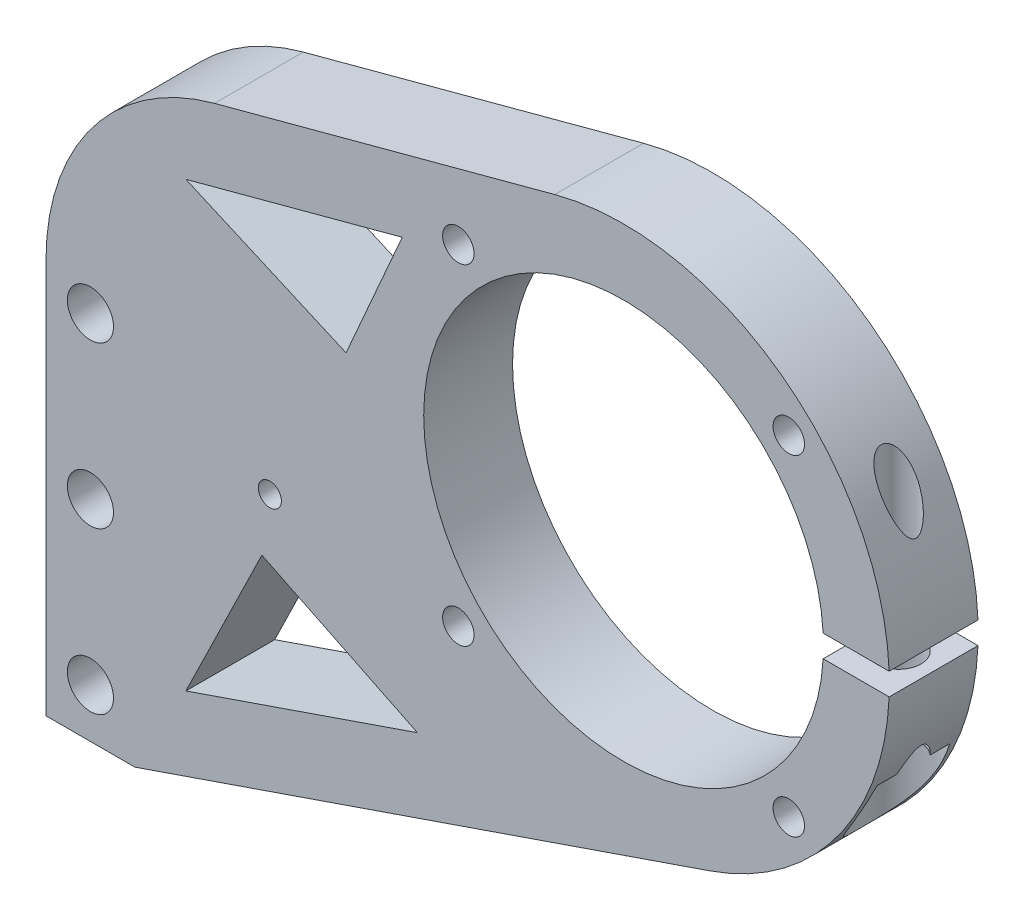
SolidWorks part; units mm, degrees
ref_plane "Front Plane" through (0, 0, 0) normal (0, 0, 1) x (1, 0, 0)
ref_plane "Top Plane" through (0, 0, 0) normal (0, 1, 0) x (1, 0, 0)
ref_plane "Right Plane" through (0, 0, 0) normal (1, 0, 0) x (0, 0, -1)
ref_plane "Plane1" through (0, 0, 0) normal (0, 0, -1) x (-1, 0, 0)
sketch "Sketch1" plane through (0, 0, 0) normal (0, 0, -1) x (-1, 0, 0)
  line L0 (224.1695, 127.7225) -> (151.4352, 147.2116)
  line L1 (129.2465, 74.5705) -> (211.4695, 46.305)
  line L2 (211.4695, 46.305) -> (224.1695, 46.305)
  line L3 (224.1695, 46.305) -> (224.1695, 127.7225)
  arc A0 (151.4352, 147.2116) -> (129.2465, 74.5705) centre (141.6001, 110.5064) ccw
extrude "Boss-Extrude1" add sketch "Sketch1" against normal blind 12.7
sketch "Sketch2" plane through (0, 0, 12.7) normal (0, 0, 1) x (1, 0, 0)
  line L0 (-103.6333, 112.0939) -> (-113.179, 112.0939)
  line L1 (-113.179, 108.9189) -> (-103.6333, 108.9189)
  arc A0 (-103.6333, 108.9189) -> (-103.6333, 112.0939) centre (-141.6001, 110.5064) ccw
  arc A1 (-113.179, 112.0939) -> (-113.179, 108.9189) centre (-141.6001, 110.5064) cw
extrude "Cut-Extrude1" cut sketch "Sketch2" against normal through all
ref_plane "Plane2" through (0, 110.5064, 0) normal (0, 1, 0) x (1, 0, 0)
sketch "Sketch3" plane through (0, 110.5064, 0) normal (0, 1, 0) x (1, 0, 0)
  line L0 (-113.0251, 0) -> (-141.6001, 0)
  line L1 (-141.6001, 0) -> (-141.6001, -12.7)
  line L2 (-141.6001, -12.7) -> (-113.0251, -12.7)
  line L3 (-113.0251, -12.7) -> (-113.0251, 0)
  line L4 (-141.6001, 0) -> (-141.6001, -12.7) construction
  dimension "D1" = 28.575
revolve "Cut-Revolve1" cut sketch "Sketch3" angle 360 about L4
hole_wizard "#8 Clearance Hole1" positions "Sketch5" profile "Sketch4" hole size "#8" standard "ANSI Inch"
sketch "Sketch5" plane through (0, 0, 12.7) normal (0, 0, 1) x (1, 0, 0)
  line L0 (-141.6001, 139.0814) -> (-141.6001, 81.9314) construction
  arc A0 (-113.0692, 112.0939) -> (-113.0692, 108.9189) centre (-141.6001, 110.5064) ccw construction
  point P0 (-117.9781, 86.8844)
  point P1 (-165.2221, 86.8844)
  point P2 (-165.2221, 134.1284)
  point P3 (-117.9781, 134.1284)
  point P12 (-141.6001, 110.5064)
  dimension "D1" = 47.244
  dimension "D2" = 47.244
  dimension "D3" = 23.622
  dimension "D4" = 47.244
  dimension "D5" = 23.622
  dimension "D6" = 23.622
  dimension "D7" = 47.244
  dimension "D8" = 23.622
sketch "Sketch4" plane through (-117.9781, 86.8844, 12.7) normal (1, 0, 0) x (0, -1, 0)
  line L0 (0, 0) -> (0, 12.7)
  line L1 (0, 12.7) -> (2.25, 12.7)
  line L2 (2.25, 12.7) -> (2.25, 0)
  line L5 (2.25, 0) -> (0, 0)
  line L11 (0, -6.35) -> (0, 107.95) construction
  dimension "Thru Hole Dia." = 4.5
  dimension "Thru Hole Depth" = 12.7
hole_wizard "1/4 Clearance Hole1" positions "Sketch7" profile "Sketch6" hole size "1/4" standard "ANSI Inch"
sketch "Sketch7" plane through (0, 0, 0) normal (0, 0, -1) x (-1, 0, 0)
  point P0 (217.8195, 53.305)
  point P1 (217.8195, 76.305)
  point P2 (217.8195, 99.305)
sketch "Sketch6" plane through (-217.8195, 53.305, 0) normal (1, 0, 0) x (0, 1, 0)
  line L0 (0, 0) -> (0, 12.7)
  line L1 (0, 12.7) -> (3.3, 12.7)
  line L2 (3.3, 12.7) -> (3.3, 0)
  line L5 (3.3, 0) -> (0, 0)
  line L11 (0, -6.35) -> (0, 107.95) construction
  dimension "Thru Hole Dia." = 6.6
  dimension "Thru Hole Depth" = 12.7
hole_wizard "#12 Clearance Hole1" positions "Sketch9" profile "Sketch8" hole size "#12" standard "ANSI Inch"
sketch "Sketch9" plane through (0, 0, 12.7) normal (0, 0, 1) x (1, 0, 0)
  point P0 (-192.1695, 89.7225)
sketch "Sketch8" plane through (-192.1695, 89.7225, 12.7) normal (1, 0, 0) x (0, -1, 0)
  line L0 (0, 0) -> (0, 12.7)
  line L1 (0, 12.7) -> (3, 12.7)
  line L2 (3, 12.7) -> (3, 0)
  line L5 (3, 0) -> (0, 0)
  line L11 (0, -6.35) -> (0, 107.95) construction
  dimension "Thru Hole Dia." = 6
  dimension "Thru Hole Depth" = 12.7
ref_plane "Plane3" through (0, 84.1425, 0) normal (0, -1, 0) x (-1, 0, 0)
hole_wizard "Hole1" positions "Sketch11" profile "Sketch10" legacy
sketch "Sketch11" plane through (0, 84.1425, 0) normal (0, -1, 0) x (-1, 0, 0)
  point P0 (108.6333, -6.35)
sketch "Sketch10" plane through (-108.6333, 84.1425, 6.35) normal (1, 0, 0) x (0, 0, -1)
  line L0 (0, 0) -> (0, 24.7764)
  line L1 (0, 24.7764) -> (3.2, 24.7764)
  line L2 (3.2, 24.7764) -> (3.2, 11.7764)
  line L3 (3.2, 11.7764) -> (5.6, 11.7764)
  line L4 (5.6, 11.7764) -> (5.6, 0)
  line L5 (5.6, 0) -> (0, 0)
  line L6 (0, 110) -> (0, -10) construction
  dimension "Diameter" = 6.4
  dimension "Depth" = 24.7764
  dimension "C-Bore Diameter" = 11.2
  dimension "C-Bore Depth" = 11.7764
hole_wizard "#10 Clearance Hole1" positions "Sketch13" profile "Sketch12" hole size "#10" standard "ANSI Inch"
sketch "Sketch13" plane through (0, 112.0939, 0) normal (0, -1, 0) x (-1, 0, 0)
  point P0 (108.6333, -6.35)
sketch "Sketch12" plane through (-108.6333, 112.0939, 6.35) normal (1, 0, 0) x (0, 0, -1)
  line L0 (0, 0) -> (0, 36.4125)
  line L1 (0, 36.4125) -> (2.5, 36.4125)
  line L2 (2.5, 36.4125) -> (2.5, 0)
  line L5 (2.5, 0) -> (0, 0)
  line L11 (0, -6.35) -> (0, 107.95) construction
  dimension "Thru Hole Dia." = 5
  dimension "Thru Hole Depth" = 36.4125
chamfer "Chamfer1" distance 3 angle 45 3 edges at (-221.1195, 53.305, 0) (-221.1195, 76.305, 0) (-221.1195, 99.305, 0)
sketch "Sketch14" plane through (0, 0, 0) normal (0, 0, -1) x (-1, 0, 0)
  circle A0 centre (192.1695, 89.7225) radius 1.651
  circle A1 centre (192.1695, 89.7225) radius 3 construction
  circle A2 centre (192.1695, 89.7225) radius 3
  point P0 (192.1695, 89.7225)
  dimension "D1" = 3.302
extrude "Boss-Extrude2" add sketch "Sketch14" against normal up to surface (12.7 mm away) up to face at (-189.1695, 89.7225, 12.7)
fillet "圆角1" radius 10 1 edges at (-224.1695, 127.7225, 6.35)
sketch "草图1" plane through (0, 0, 0) normal (0, 0, -1) x (-1, 0, 0)
  line L0 (216.7576, 129.7085) -> (151.4352, 147.2116) construction
  line L1 (216.7576, 129.7085) -> (200.0811, 134.177)
  line L2 (224.1695, 46.305) -> (224.1695, 120.0493) construction
  line L3 (224.1695, 102.7844) -> (224.1695, 120.0493)
  arc A0 (224.1695, 102.7844) -> (200.0811, 134.177) centre (191.6695, 102.7844) ccw
  dimension "D1" = 65
extrude "切除-拉伸1" cut sketch "草图1" against normal through all and the other way through all
sketch "草图2" plane through (0, 0, 0) normal (0, 0, -1) x (-1, 0, 0)
  line L0 (171.0706, 70.7672) -> (204.1695, 59.3889)
  line L1 (204.1695, 59.3889) -> (193.3092, 81.6275)
  line L2 (193.3092, 81.6275) -> (171.0706, 70.7672)
  line L3 (181.2708, 112.6961) -> (173.2447, 131.015)
  line L4 (173.2447, 131.015) -> (204.1695, 122.7288)
  line L5 (204.1695, 122.7288) -> (181.2708, 112.6961)
  line L6 (200.0811, 134.177) -> (151.4352, 147.2116) construction
  line L7 (129.2465, 74.5705) -> (211.4695, 46.305) construction
  line L8 (224.1695, 46.305) -> (224.1695, 102.7844) construction
  dimension "D1" = 35
  dimension "D2" = 10
  dimension "D3" = 10
  dimension "D4" = 20
  dimension "D5" = 20
  dimension "D6" = 25
  dimension "D7" = 20
extrude "切除-拉伸2" cut sketch "草图2" against normal through all
